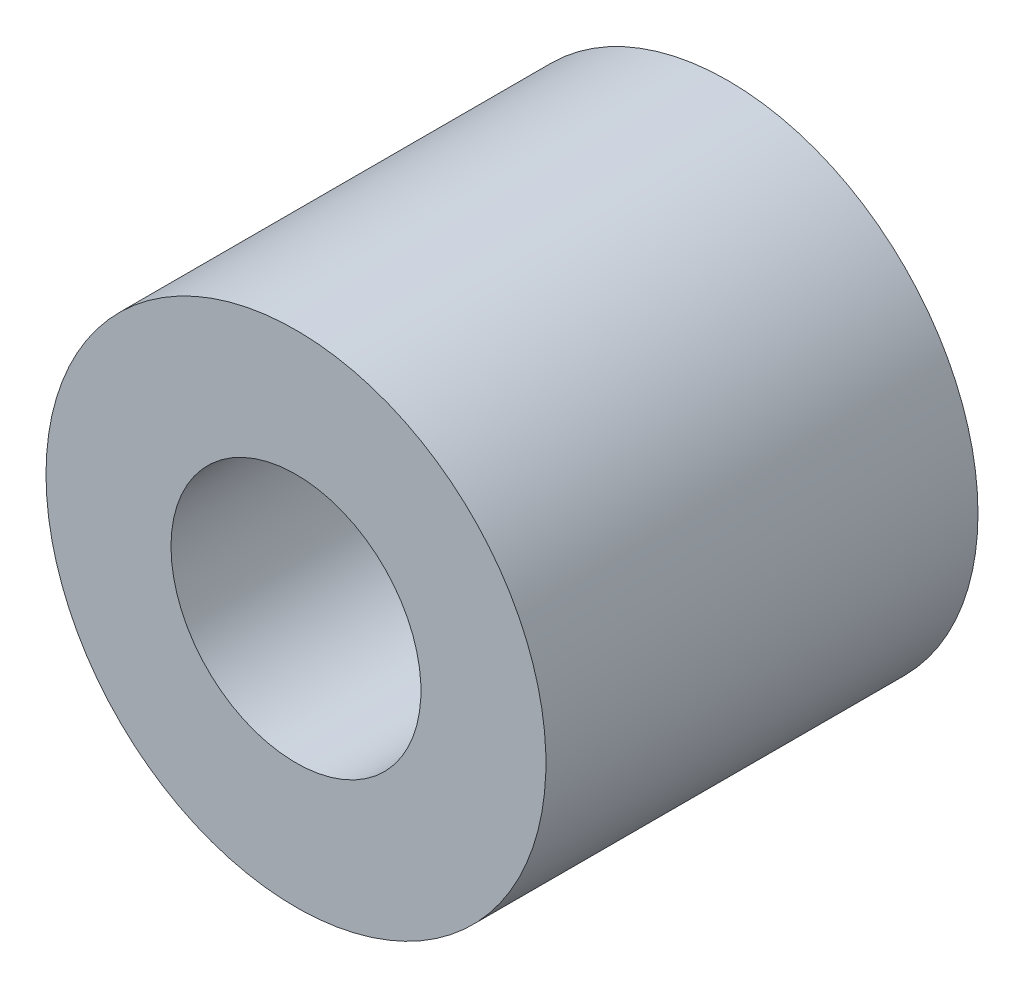
SolidWorks part; units mm, degrees
material "Plastique personnalisé"
ref_plane "Plan de face" through (0, 0, 0) normal (0, 0, 1) x (1, 0, 0)
ref_plane "Plan de dessus" through (0, 0, 0) normal (0, 1, 0) x (1, 0, 0)
ref_plane "Plan de droite" through (0, 0, 0) normal (1, 0, 0) x (0, 0, -1)
sketch "Esquisse1" plane through (0, 0, 0) normal (0, 0, 1) x (1, 0, 0)
  circle A0 centre (0, 0) radius 1.75
  circle A1 centre (0, 0) radius 3.5
extrude "Boss.-Extru.1" add sketch "Esquisse1" along normal up to surface (6.05 mm away)
